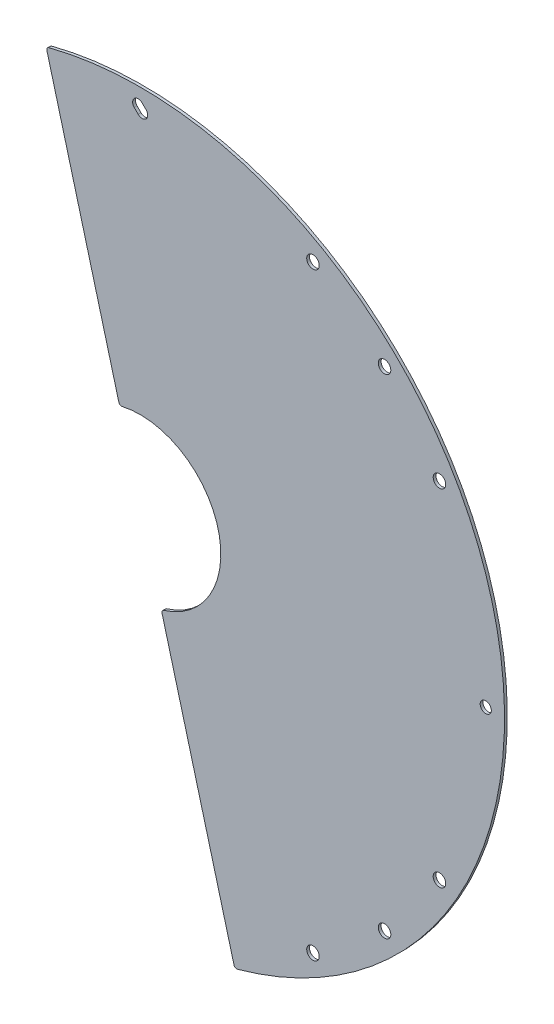
SolidWorks part; units mm, degrees
material "Hexcel AS4C (3000 Filaments)"
ref_plane "Front" through (0, 0, 0) normal (0, 0, 1) x (1, 0, 0)
ref_plane "Top" through (0, 0, 0) normal (0, 1, 0) x (1, 0, 0)
ref_plane "Right" through (0, 0, 0) normal (1, 0, 0) x (0, 0, -1)
sketch "Sketch1" plane through (0, 0, 0) normal (1, 0, 0) x (0, 0, -1)
  line L0 (0, 0) -> (34.5798, 0) construction
  line L1 (0, 131) -> (0, 29)
  dimension "D4" = 29
  dimension "D5" = 131
revolve "Revolve-Thin1" add sketch "Sketch1" angle 15 about L0
hole_wizard "Ø4.5 (4.5) Diameter Hole1" positions "Sketch5" profile "Sketch6" hole size "Ø4.5" standard "Ansi Metric" end condition through all
sketch "Sketch5" plane through (0, 0, 1) normal (0, 0, 1) x (1, 0, 0)
  line L0 (62.125, 107.6037) -> (0, 0)
  line L2 (0, -7.8423) -> (0, 42.4304) construction
  point P0 (62.125, 107.6037)
  dimension "D1" = 124.25
  dimension "D2" = 30
sketch "Sketch6" plane through (62.125, 107.6037, 1) normal (1, 0, 0) x (0, -1, 0)
  line L0 (0, 0) -> (0, 1)
  line L1 (0, 1) -> (2.25, 1)
  line L2 (2.25, 1) -> (2.25, 0)
  line L5 (2.25, 0) -> (0, 0)
  line L11 (0, -6.35) -> (0, 107.95) construction
  dimension "Thru Hole Dia." = 4.5
  dimension "Thru Hole Depth" = 1
ref_axis "Axis1" through (0, 0, -80.9) along (0, 0, 1)
pattern_circular "CirPattern1" count 12 over 360 about axis through (0, 0, -80.9) along (0, 0, 1) skipping 1, 2, 3, 4, 5, 6, 7, 10 of "Ø4.5 (4.5) Diameter Hole1"
hole_wizard "Ø4.0 (4) Diameter Hole1" positions "Sketch8" profile "Sketch7" hole size "Ø4.0" standard "Ansi Metric" end condition through all
sketch "Sketch8" plane through (0, 0, 1) normal (0, 0, 1) x (1, 0, 0)
  line L0 (0, 0) -> (124.25, 0)
  line L2 (0, 0) -> (107.6037, 62.125)
  point P0 (124.25, 0)
sketch "Sketch7" plane through (124.25, 0, 1) normal (1, 0, 0) x (0, -1, 0)
  line L0 (0, 0) -> (0, 1)
  line L1 (0, 1) -> (2, 1)
  line L2 (2, 1) -> (2, 0)
  line L5 (2, 0) -> (0, 0)
  line L11 (0, -6.35) -> (0, 107.95) construction
  dimension "Thru Hole Dia." = 4
  dimension "Thru Hole Depth" = 1
pattern_circular "CirPattern2" count 4 over 360 about axis through (0, 0, -80.9) along (0, 0, 1) skipping 2, 3 of "Ø4.0 (4) Diameter Hole1"
hole_wizard "Ø4.5 (4.5) Diameter Hole2" positions "Sketch10" profile "Sketch11" hole size "Ø4.5" standard "Ansi Metric" end condition through all
sketch "Sketch10" plane through (0, 0, 1) normal (0, 0, 1) x (1, 0, 0)
  line L0 (0, 0) -> (87.858, 87.858)
  line L2 (0, 124.25) -> (0, 0)
  point P0 (87.858, 87.858)
  dimension "D1" = 45
sketch "Sketch11" plane through (87.858, 87.858, 1) normal (1, 0, 0) x (0, -1, 0)
  line L0 (0, 0) -> (0, 1)
  line L1 (0, 1) -> (2.25, 1)
  line L2 (2.25, 1) -> (2.25, 0)
  line L5 (2.25, 0) -> (0, 0)
  line L11 (0, -6.35) -> (0, 107.95) construction
  dimension "Thru Hole Dia." = 4.5
  dimension "Thru Hole Depth" = 1
pattern_circular "CirPattern3" count 2 every 90 about axis through (0, 0, -80.9) along (0, 0, 1) of "Ø4.5 (4.5) Diameter Hole2"
sketch "Sketch12" plane through (0, 0, 1) normal (0, 0, 1) x (1, 0, 0)
  line L0 (-0.7071, 124.9571) -> (0.7071, 123.5429) construction
  line L1 (0.7071, 126.3713) -> (2.1213, 124.9571)
  line L2 (-2.1213, 123.5429) -> (-0.7071, 122.1287)
  line L3 (0.7071, 123.5429) -> (124.25, 0) construction
  arc A0 (0.7071, 126.3713) -> (-2.1213, 123.5429) centre (-0.7071, 124.9571) ccw
  arc A1 (-0.7071, 122.1287) -> (2.1213, 124.9571) centre (0.7071, 123.5429) ccw
  circle A2 centre (0, 124.25) radius 2 construction
  point P2 (0, 124.25)
  dimension "D1" = 2
extrude "Cut-Extrude1" cut sketch "Sketch12" against normal through all
sketch "Sketch13" plane through (0, 0, 1) normal (0, 0, 1) x (1, 0, 0)
  line L0 (-33.9053, 126.5363) -> (33.9053, -126.5363)
  line L1 (-33.9053, 126.5363) -> (-33.8087, 126.5622)
  line L2 (33.9053, -126.5363) -> (34.0019, -126.5104)
  line L3 (-33.8087, 126.5622) -> (34.0019, -126.5104)
  dimension "D1" = 0.1
extrude "Cut-Extrude2" cut sketch "Sketch13" against normal through all
fillet "Fillet1" radius 1 4 edges at (34.0019, -126.5104, 0.5) (-33.8087, 126.5621, 0.5) (7.6023, -27.9858, 0.5) (-7.4091, 28.0376, 0.5)
